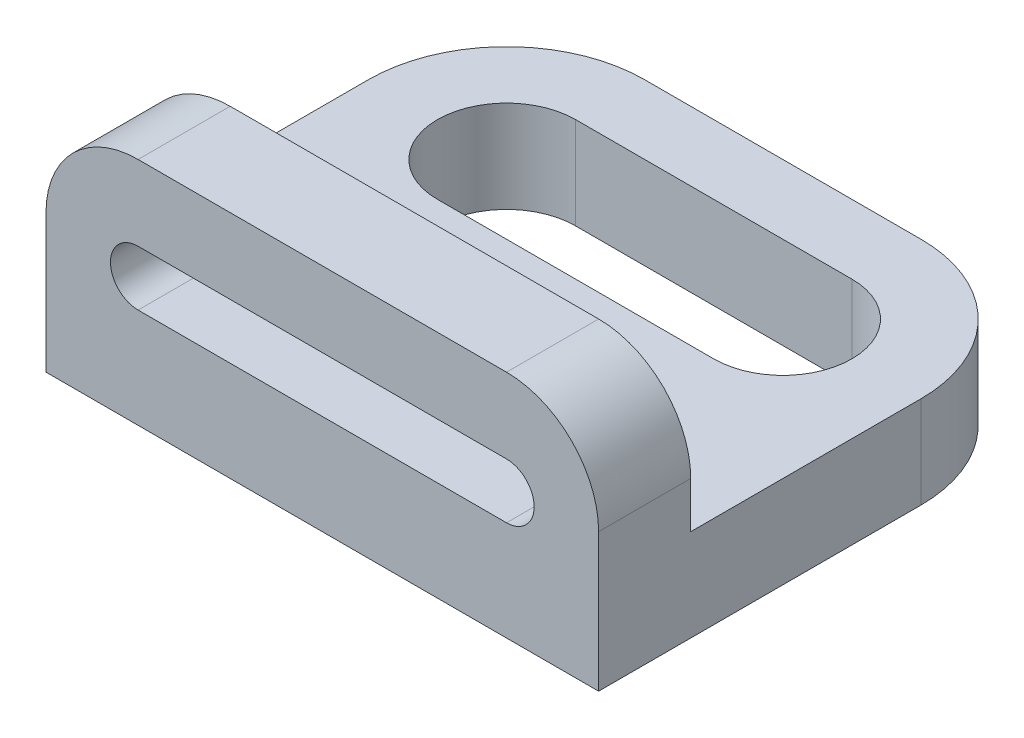
SolidWorks part; units mm, degrees
ref_plane "Front Plane" through (0, 0, 0) normal (0, 0, 1) x (1, 0, 0)
ref_plane "Top Plane" through (0, 0, 0) normal (0, 1, 0) x (1, 0, 0)
ref_plane "Right Plane" through (0, 0, 0) normal (1, 0, 0) x (0, 0, -1)
sketch "Sketch1" plane through (0, 0, 0) normal (1, 0, 0) x (0, 0, -1)
  line L0 (-30, 25) -> (-30, -5)
  line L1 (-50, -25) -> (50, -25)
  line L2 (-50, -25) -> (-50, 25)
  line L3 (-50, 25) -> (-30, 25)
  line L4 (50, -25) -> (50, -5)
  line L7 (-30, -5) -> (50, -5)
  line L8 (0, 0) -> (10, -5) construction
  line L9 (-10, -5) -> (0, 0) construction
  point P0 (0, 0)
  dimension "D1" = 50
  dimension "D2" = 100
  dimension "D3" = 20
  dimension "D4" = 20
extrude "Boss-Extrude1" add sketch "Sketch1" along normal blind 120
fillet "Fillet1" radius 20 2 edges at (0, 25, 40) (120, 25, 40)
fillet "Fillet2" radius 30 2 edges at (120, -15, -50) (0, -15, -50)
sketch "Sketch2" plane through (0, -5, 0) normal (0, 1, 0) x (1, 0, 0)
  line L0 (-17.5017, 20) -> (129.6394, 20) construction
  line L1 (100, -50) -> (20, -50) construction
  line L2 (30, 52.2638) -> (30, -4.4907) construction
  line L3 (90, 55.1302) -> (90, -4.4907) construction
  line L4 (120, 20) -> (120, -30) construction
  line L5 (30, 20) -> (90, 20) construction
  line L6 (30, 35) -> (90, 35)
  line L7 (30, 5) -> (90, 5)
  arc A0 (30, 35) -> (30, 5) centre (30, 20) ccw
  arc A1 (90, 5) -> (90, 35) centre (90, 20) ccw
  point P12 (60, 20)
  dimension "D4" = 15
  dimension "D1" = 70
  dimension "D2" = 30
  dimension "D3" = 60
extrude "Cut-Extrude1" cut sketch "Sketch2" against normal through all
sketch "Sketch3" plane through (0, 0, 30) normal (0, 0, -1) x (-1, 0, 0)
  line L0 (-100, 29.0009) -> (-100, -2.5128) construction
  line L1 (-20, 31.5961) -> (-20, 0) construction
  line L2 (-120, 2.6777) -> (6.7138, 2.6777)
  line L5 (-120, -5) -> (-120, 5) construction
  line L6 (-100, 2.6777) -> (-20, 2.6777) construction
  line L7 (-100, 8.6777) -> (-20, 8.6777)
  line L8 (-100, -3.3223) -> (-20, -3.3223)
  arc A0 (-100, 8.6777) -> (-100, -3.3223) centre (-100, 2.6777) ccw
  arc A1 (-20, -3.3223) -> (-20, 8.6777) centre (-20, 2.6777) ccw
  point P9 (-60, 2.6777)
  dimension "D3" = 6
  dimension "D1" = 20
  dimension "D2" = 80
extrude "Cut-Extrude3" cut sketch "Sketch3" against normal through all contours A1 L7 A0 L8
